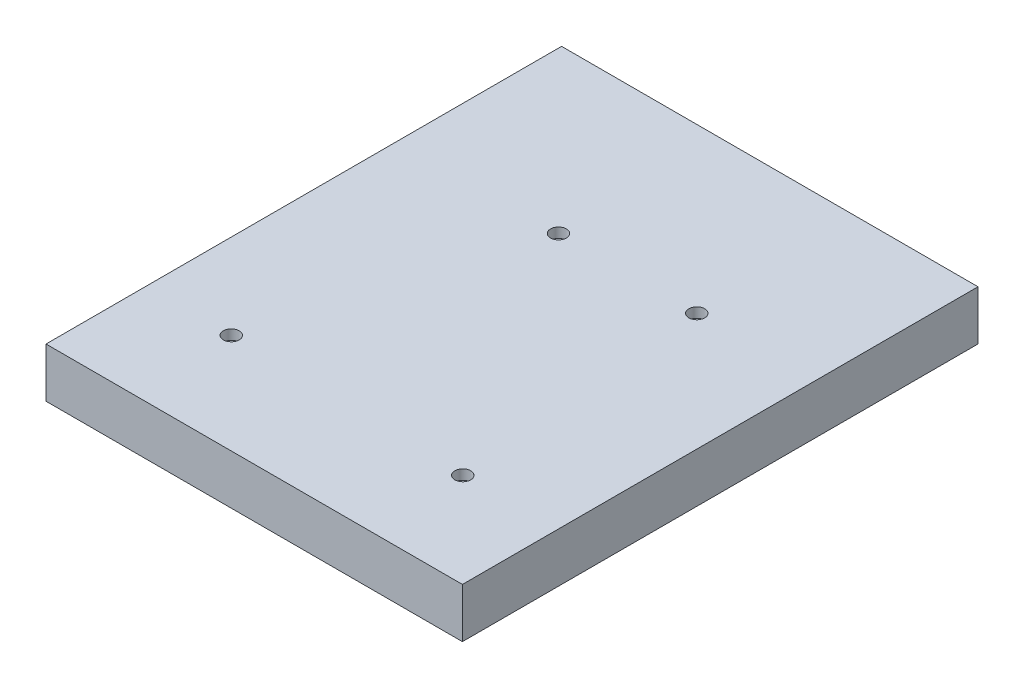
SolidWorks part; units mm, degrees
ref_plane "Front Plane" through (0, 0, 0) normal (0, 0, 1) x (1, 0, 0)
ref_plane "Top Plane" through (0, 0, 0) normal (0, 1, 0) x (1, 0, 0)
ref_plane "Right Plane" through (0, 0, 0) normal (1, 0, 0) x (0, 0, -1)
sketch "Sketch1" plane through (0, 0, 0) normal (0, 1, 0) x (1, 0, 0)
  line L1 (-42, 52) -> (42, 52)
  line L2 (-42, 52) -> (-42, -52)
  line L3 (-42, -52) -> (42, -52)
  line L4 (42, 52) -> (42, -52)
  line L5 (-42, 52) -> (42, -52) construction
  line L6 (-42, -52) -> (42, 52) construction
  point P0 (0, 0)
  dimension "D1" = 84
  dimension "D2" = 104
extrude "Boss-Extrude1" add sketch "Sketch1" along normal blind 20
ref_plane "Plane1" through (0, 0, 0) normal (0, -1, 0) x (-1, 0, 0)
sketch "Sketch2" plane through (0, 0, 0) normal (0, -1, 0) x (-1, 0, 0)
  line L0 (-42, 52) -> (42, 52) construction
  line L1 (-41, 51) -> (41, 51)
  line L2 (-41, 51) -> (-41, -51)
  line L3 (-41, -51) -> (41, -51)
  line L4 (41, 51) -> (41, -51)
  line L5 (-41, 51) -> (41, -51) construction
  line L6 (-41, -51) -> (41, 51) construction
  line L7 (42, 52) -> (42, -52) construction
  point P0 (0, 0)
  dimension "D1" = 1
  dimension "D2" = 1
extrude "Cut-Extrude1" cut sketch "Sketch2" against normal blind 5
ref_plane "Plane2" through (0, 20, 0) normal (0, 1, 0) x (1, 0, 0)
sketch "Sketch3" plane through (0, 20, 0) normal (0, 1, 0) x (1, 0, 0)
  line L0 (42, 52) -> (-42, 52) construction
  line L1 (-37, 47) -> (37, 47)
  line L2 (-37, 47) -> (-37, -47)
  line L3 (-37, -47) -> (37, -47)
  line L4 (37, 47) -> (37, -47)
  line L5 (-37, 47) -> (37, -47) construction
  line L6 (-37, -47) -> (37, 47) construction
  line L7 (42, -52) -> (42, 52) construction
  point P0 (0, 0)
  dimension "D1" = 5
  dimension "D2" = 5
extrude "Cut-Extrude2" cut sketch "Sketch3" against normal blind 10
ref_plane "Plane3" through (0, 0, -47) normal (0, 0, 1) x (1, 0, 0)
sketch "Sketch4" plane through (0, 0, -47) normal (0, 0, 1) x (1, 0, 0)
  line L0 (37, 10) -> (-37, 10) construction
  line L1 (-22.86, 10) -> (22.86, 10)
  line L2 (-22.86, 10) -> (-22.86, 20)
  line L3 (-22.86, 20) -> (22.86, 20)
  line L4 (22.86, 10) -> (22.86, 20)
  line L5 (37, 20) -> (-37, 20) construction
  line L6 (-37, 10) -> (-37, 20) construction
  line L11 (-22.86, 10) -> (-18.86, 10)
  line L12 (-22.86, 10) -> (-22.86, 20)
  line L13 (-22.86, 20) -> (-18.86, 20)
  line L14 (-18.86, 10) -> (-18.86, 20)
  line L15 (22.86, 10) -> (18.86, 10)
  line L16 (22.86, 10) -> (22.86, 20)
  line L17 (22.86, 20) -> (18.86, 20)
  line L18 (18.86, 10) -> (18.86, 20)
  dimension "D1" = 45.72
  dimension "D2" = 14.14
  dimension "D3" = 4
  dimension "D4" = 10
  dimension "D5" = 4
  dimension "D6" = 10
extrude "Cut-Extrude4" cut sketch "Sketch4" against normal through all contours L1 L18 L3 L14
ref_plane "Plane4" through (0, 0, 47) normal (0, 0, -1) x (-1, 0, 0)
sketch "Sketch6" plane through (0, 0, 47) normal (0, 0, -1) x (-1, 0, 0)
  line L0 (37, 10) -> (-37, 10) construction
  line L1 (3.65, 10) -> (18.65, 10)
  line L2 (3.65, 10) -> (3.65, 20)
  line L3 (3.65, 20) -> (18.65, 20)
  line L4 (18.65, 10) -> (18.65, 20)
  line L5 (37, 20) -> (-37, 20) construction
  line L8 (-37, 10) -> (-37, 20) construction
  line L9 (-26.65, 20) -> (26.65, 20)
  line L10 (-26.65, 20) -> (-26.65, 10)
  line L11 (-26.65, 10) -> (26.65, 10)
  line L12 (26.65, 20) -> (26.65, 10)
  line L13 (-26.65, 20) -> (26.65, 10) construction
  line L14 (-26.65, 10) -> (26.65, 20) construction
  line L16 (-22.35, 10) -> (-12.35, 10)
  line L17 (-22.35, 10) -> (-22.35, 20)
  line L18 (-22.35, 20) -> (-12.35, 20)
  line L19 (-12.35, 10) -> (-12.35, 20)
  point P8 (0, 15)
  dimension "D1" = 15
  dimension "D2" = 8
  dimension "D3" = 16
  dimension "D4" = 10.35
  dimension "D5" = 53.3
  dimension "D6" = 10
extrude "Cut-Extrude6" cut sketch "Sketch6" against normal blind 10 contours L1 L4 L3 L2 | L17 L16 L19 L18
ref_plane "Plane5" through (0, 10, 0) normal (0, 1, 0) x (1, 0, 0)
sketch "Sketch7" plane through (0, 10, 0) normal (0, 1, 0) x (1, 0, 0)
  line L0 (-37, -47) -> (-18.65, -47) construction
  line L1 (-27.825, -47) -> (25.475, -47)
  line L2 (-27.825, -47) -> (-27.825, 21.6)
  line L3 (-27.825, 21.6) -> (25.475, 21.6)
  line L4 (25.475, -47) -> (25.475, 21.6)
  circle A0 centre (-24.825, -31.8) radius 1.6
  circle A1 centre (22.975, -32.9) radius 1.6
  circle A2 centre (-9.625, 19) radius 1.6
  circle A3 centre (18.275, 19) radius 1.6
  dimension "D3" = 3.2
  dimension "D4" = 3
  dimension "D6" = 3.2
  dimension "D7" = 14.1
  dimension "D8" = 2.5
  dimension "D9" = 3.2
  dimension "D10" = 2.6
  dimension "D11" = 18.2
  dimension "D12" = 3.2
  dimension "D13" = 7.2
  dimension "D14" = 2.6
  dimension "D1" = 53.3
  dimension "D2" = 68.6
  dimension "D5" = 15.2
extrude "Cut-Extrude7" cut sketch "Sketch7" against normal blind 2 contours A3 | A0 | A1 | A2
ref_plane "Plane6" through (37, 0, 0) normal (-1, 0, 0) x (0, 0, 1)
sketch "Sketch9" plane through (-42, 0, 0) normal (-1, 0, 0) x (0, 0, 1)
  line L0 (47, 5.5) -> (47, -5.5) construction
  line L1 (-52, 20) -> (52, 20)
  line L2 (-52, 20) -> (-52, 10)
  line L3 (-52, 10) -> (52, 10)
  line L4 (52, 20) -> (52, 10)
  dimension "D1" = 5
  dimension "D2" = 10
extrude "Cut-Extrude8" cut sketch "Sketch9" against normal through all contours L2 L1 L4 L3
